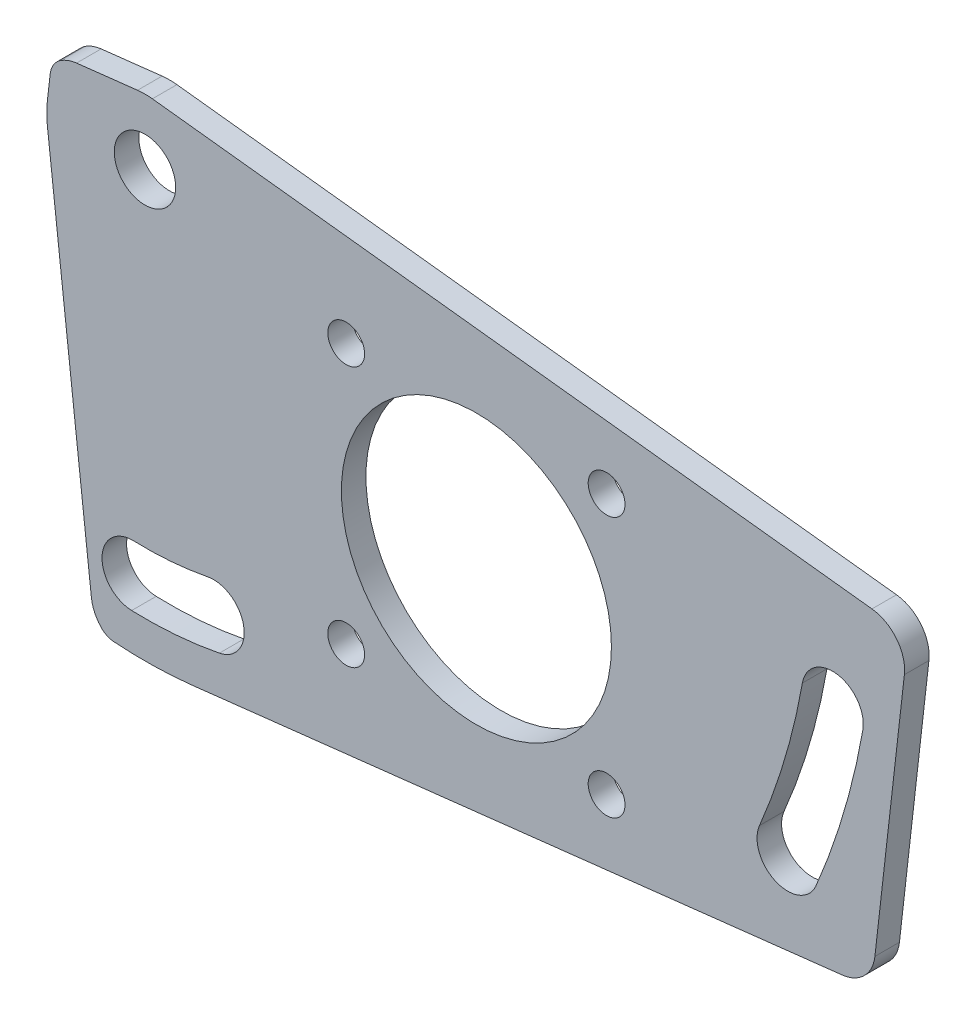
SolidWorks part; units mm, degrees
ref_plane "Płaszczyzna przednia" through (0, 0, 0) normal (0, 0, 1) x (1, 0, 0)
ref_plane "Płaszczyzna górna" through (0, 0, 0) normal (0, 1, 0) x (1, 0, 0)
ref_plane "Płaszczyzna prawa" through (0, 0, 0) normal (1, 0, 0) x (0, 0, -1)
sketch "Szkic1" plane through (0, 0, 0) normal (0, 0, 1) x (1, 0, 0)
  line L0 (25.3611, -7.5593) -> (-27, 14.6667) construction
  line L1 (-32, -20) -> (32, -20)
  line L2 (-35, -17) -> (-35, 17)
  line L3 (-32, 20) -> (32, 20)
  line L4 (35, -17) -> (35, 17)
  line L5 (-35, -20) -> (35, 20) construction
  line L6 (-35, 20) -> (35, -20) construction
  line L7 (-27, 14.6667) -> (29.0188, 4.789) construction
  line L10 (-28, -14.4829) -> (-27, 14.6667) construction
  line L11 (-27, 14.6667) -> (-21.4172, -13.9607) construction
  arc A0 (-32, -20) -> (-35, -17) centre (-32, -17) cw
  arc A1 (32, -20) -> (35, -17) centre (32, -17) ccw
  arc A2 (32, 20) -> (35, 17) centre (32, 17) cw
  arc A3 (-35, 17) -> (-32, 20) centre (-32, 17) cw
  circle A4 centre (0, 0) radius 11
  circle A5 centre (-27, 14.6667) radius 2.5
  arc A6 (25.3611, -7.5593) -> (29.0188, 4.789) centre (-27, 14.6667) ccw construction
  arc A7 (27.6623, -8.5361) -> (31.4808, 4.3549) centre (-27, 14.6667) ccw
  arc A8 (23.0598, -6.5825) -> (26.5568, 5.2232) centre (-27, 14.6667) ccw
  arc A9 (23.0598, -6.5825) -> (27.6623, -8.5361) centre (25.3611, -7.5593) ccw
  arc A10 (31.4808, 4.3549) -> (26.5568, 5.2232) centre (29.0188, 4.789) ccw
  arc A13 (-28, -14.4829) -> (-21.4172, -13.9607) centre (-27, 14.6667) ccw construction
  arc A14 (-28.0857, -16.9814) -> (-20.9386, -16.4145) centre (-27, 14.6667) ccw
  arc A15 (-27.9143, -11.9843) -> (-21.8957, -11.5069) centre (-27, 14.6667) ccw
  arc A16 (-27.9143, -11.9843) -> (-28.0857, -16.9814) centre (-28, -14.4829) ccw
  arc A17 (-20.9386, -16.4145) -> (-21.8957, -11.5069) centre (-21.4172, -13.9607) ccw
  point P0 (0, 0)
  point P25 (27.5405, -1.489)
  point P35 (-24.6938, -14.4087)
  point P36 (27.5405, -1.489)
  dimension "D3" = 3
  dimension "D4" = 5
  dimension "D5" = 22
  dimension "D7" = 2.5
  dimension "D8" = 3
  dimension "D9" = 10
  dimension "D10" = 13
  dimension "D12" = 2.5
  dimension "D11" = 4.5
  dimension "D1" = 70
  dimension "D2" = 40
  dimension "D6" = 13
extrude "Dodanie-wyciągnięcie1" add sketch "Szkic1" along normal blind 2
sketch "Szkic2" plane through (0, 0, 0) normal (0, 0, 1) x (1, 0, 0)
  line L2 (-10.6066, -10.6066) -> (10.6066, -10.6066) construction
  line L3 (-10.6066, -10.6066) -> (-10.6066, 10.6066) construction
  line L4 (-10.6066, 10.6066) -> (10.6066, 10.6066) construction
  line L5 (10.6066, -10.6066) -> (10.6066, 10.6066) construction
  line L6 (-10.6066, -10.6066) -> (10.6066, 10.6066) construction
  line L7 (-10.6066, 10.6066) -> (10.6066, -10.6066) construction
  circle A0 centre (-10.6066, 10.6066) radius 1.5
  circle A1 centre (10.6066, 10.6066) radius 1.5
  circle A2 centre (10.6066, -10.6066) radius 1.5
  circle A3 centre (-10.6066, -10.6066) radius 1.5
  point P11 (0, 0)
  dimension "D1" = 3
  dimension "D2" = 30
extrude "Wytnij-wyciągnięcie2" cut sketch "Szkic2" along normal through all
sketch "Szkic3" plane through (0, 0, 0) normal (0, 0, 1) x (1, 0, 0)
  line L0 (32.4644, -11.109) -> (34.8656, 9.9664)
  line L1 (-34.7231, 17.5512) -> (-34.9486, 15.5723)
  line L2 (32.2245, 13.2867) -> (-26.3962, 19.9657)
  line L9 (-23.0756, -19.7772) -> (29.8233, -13.7501)
  line L11 (-27.6038, 19.9657) -> (-32.5716, 19.3997)
  line L12 (-34.9486, 13.761) -> (-31.3638, -17.7021)
  arc A2 (34.8656, 9.9664) -> (32.2245, 13.2867) centre (31.8849, 10.306) ccw
  arc A4 (-26.3962, 19.9657) -> (-27.6038, 19.9657) centre (-27, 14.6667) ccw
  arc A5 (-33.8699, 18.9324) -> (-34.7231, 17.5512) centre (-32.8292, 17.3354) ccw
  arc A6 (-34.9486, 15.5723) -> (-34.9486, 13.761) centre (-27, 14.6667) ccw
  arc A7 (-29.5516, -19.906) -> (-23.0756, -19.7772) centre (-27, 14.6667) ccw
  arc A8 (-31.3638, -17.7021) -> (-30.5562, -19.4307) centre (-28.3831, -17.3625) ccw
  arc A11 (-32.5716, 19.3997) -> (-33.8699, 18.9324) centre (-32.232, 16.419) ccw
  arc A12 (29.8233, -13.7501) -> (32.4644, -11.109) centre (29.4836, -10.7694) ccw
  arc A13 (-30.5562, -19.4307) -> (-29.5516, -19.906) centre (-29.438, -18.3665) ccw
  point P0 (-27, 14.6667)
  point P1 (-27, 14.6667)
  dimension "D1" = 3
extrude "Wytnij-wyciągnięcie3" cut sketch "Szkic3" along normal through all flip side to cut
chamfer "Sfazowanie1" [suppressed] distance 2 angle 45
chamfer "Sfazowanie2" [suppressed] distance 0.1 angle 45
